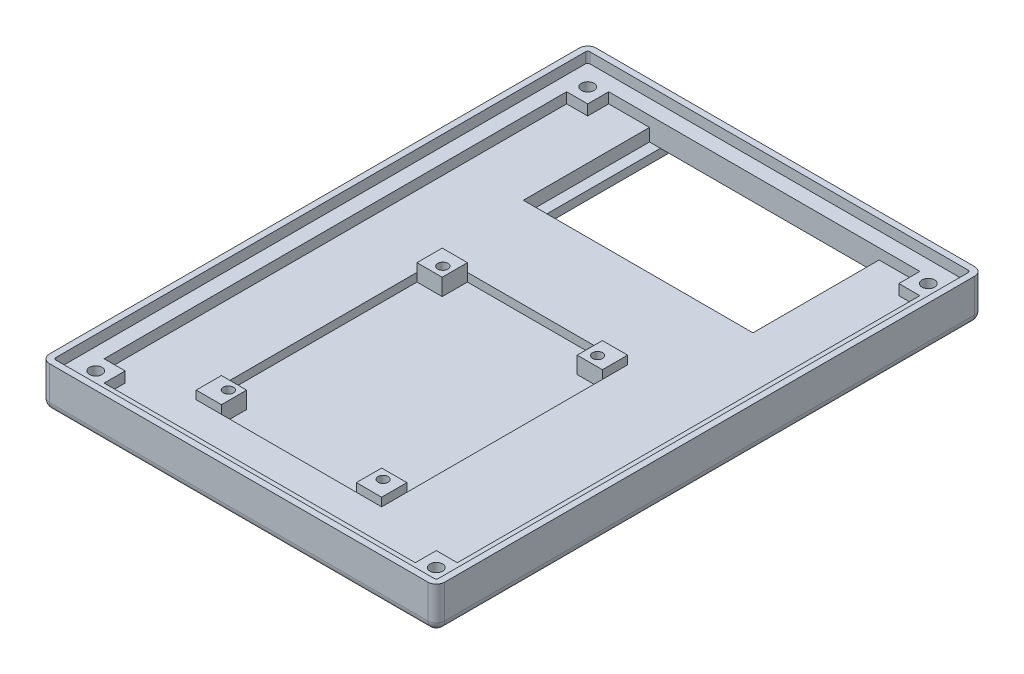
SolidWorks part; units mm, degrees
ref_plane "Front Plane" through (0, 0, 0) normal (0, 0, 1) x (1, 0, 0)
ref_plane "Top Plane" through (0, 0, 0) normal (0, 1, 0) x (1, 0, 0)
ref_plane "Right Plane" through (0, 0, 0) normal (1, 0, 0) x (0, 0, -1)
sketch "Sketch1" plane through (0, 0, 0) normal (0, 1, 0) x (1, 0, 0)
  line L1 (0, 0) -> (94, 0)
  line L2 (0, 0) -> (0, 130)
  line L3 (0, 130) -> (94, 130)
  line L4 (94, 0) -> (94, 130)
  dimension "D1" = 94
  dimension "D2" = 130
extrude "Boss-Extrude1" add sketch "Sketch1" along normal blind 5
sketch "Sketch2" plane through (0, 5, 0) normal (0, 1, 0) x (1, 0, 0)
  line L4 (5, 125) -> (5, 5)
  line L5 (5, 5) -> (89, 5)
  line L6 (89, 5) -> (89, 125)
  line L7 (89, 125) -> (5, 125)
  line L8 (0, 130) -> (0, 0)
  line L9 (0, 0) -> (94, 0)
  line L10 (94, 0) -> (94, 130)
  line L11 (94, 130) -> (0, 130)
  line L12 (0, 130) -> (0, 0)
  line L13 (0, 0) -> (94, 0)
  line L14 (94, 0) -> (94, 130)
  line L15 (94, 130) -> (0, 130)
  dimension "D1" = 0
  dimension "D2" = 5
extrude "Boss-Extrude2" add sketch "Sketch2" along normal blind 5
fillet "Fillet1" radius 2 8 edges at (0, 5, -130) (0, 5, 0) (94, 5, 0) (47, 0, 0) (0, 0, -65) (94, 0, -65) (47, 0, -130) (94, 5, -130)
sketch "Sketch3" plane through (0, 5, 0) normal (0, 1, 0) x (1, 0, 0)
  line L0 (5, 125) -> (5, 5) construction
  line L1 (21.9, 73.5) -> (66, 73.5)
  line L2 (21.9, 73.5) -> (21.9, 15)
  line L3 (21.9, 15) -> (66, 15)
  line L4 (66, 73.5) -> (66, 15)
  line L11 (5, 5) -> (89, 5) construction
  dimension "D1" = 58.5
  dimension "D2" = 44.1
  dimension "D3" = 16.9
  dimension "D4" = 10
extrude "Cut-Extrude1" cut sketch "Sketch3" against normal blind 2
sketch "Sketch5" plane through (0, 3, 0) normal (0, 1, 0) x (1, 0, 0)
  line L0 (66, 73.5) -> (21.9, 73.5) construction
  line L1 (21.9, 73.5) -> (27.9, 73.5)
  line L2 (21.9, 73.5) -> (21.9, 67.5)
  line L3 (21.9, 67.5) -> (27.9, 67.5)
  line L4 (27.9, 73.5) -> (27.9, 67.5)
  line L5 (60, 73.5) -> (66, 73.5)
  line L6 (60, 73.5) -> (60, 67.5)
  line L7 (60, 67.5) -> (66, 67.5)
  line L8 (66, 73.5) -> (66, 67.5)
  line L9 (60, 21) -> (66, 21)
  line L10 (60, 21) -> (60, 15)
  line L11 (60, 15) -> (66, 15)
  line L12 (66, 21) -> (66, 15)
  line L13 (21.9, 21) -> (27.9, 21)
  line L14 (21.9, 21) -> (21.9, 15)
  line L15 (21.9, 15) -> (27.9, 15)
  line L16 (27.9, 21) -> (27.9, 15)
  line L17 (21.9, 73.5) -> (21.9, 15) construction
  line L18 (66, 15) -> (66, 73.5) construction
  line L19 (21.9, 15) -> (66, 15) construction
  dimension "D1" = 6
  dimension "D2" = 6
  dimension "D3" = 6
  dimension "D4" = 6
  dimension "D5" = 6
  dimension "D6" = 6
  dimension "D7" = 6
  dimension "D8" = 6
extrude "Boss-Extrude4" add sketch "Sketch5" along normal blind 4
sketch "Sketch7" plane through (0, 7, 0) normal (0, 1, 0) x (1, 0, 0)
  circle A0 centre (25.71, 69.839) radius 1.2
  circle A1 centre (62.5146, 69.839) radius 1.2
  circle A2 centre (62.5146, 18.8358) radius 1.2
  circle A3 centre (25.71, 18.8358) radius 1.2
  point P1 (0, 0)
  point P12 (0, 0)
  point P14 (0, 0)
  point P16 (0, 0)
  point P18 (0, 0)
extrude "Cut-Extrude2" cut sketch "Sketch7" against normal blind 3
sketch "Sketch8" plane through (0, 5, 0) normal (0, 1, 0) x (1, 0, 0)
  line L1 (19.7, 95) -> (74.3, 95)
  line L2 (19.7, 95) -> (19.7, 125)
  line L3 (19.7, 125) -> (74.3, 125)
  line L4 (74.3, 95) -> (74.3, 125)
  line L5 (89, 125) -> (5, 125) construction
  line L6 (89, 125) -> (5, 125) construction
  point P4 (47, 125)
  point P9 (47, 95)
  dimension "D1" = 30
  dimension "D2" = 54.6
extrude "Cut-Extrude3" cut sketch "Sketch8" against normal blind 3
sketch "Sketch9" plane through (0, 2, 0) normal (0, 1, 0) x (1, 0, 0)
  line L0 (19.7, 95) -> (74.3, 95) construction
  line L1 (22.3, 96.5) -> (71.7, 96.5)
  line L2 (22.3, 96.5) -> (22.3, 123.5)
  line L3 (22.3, 123.5) -> (71.7, 123.5)
  line L4 (71.7, 96.5) -> (71.7, 123.5)
  line L5 (74.3, 125) -> (19.7, 125) construction
  line L6 (19.7, 125) -> (19.7, 95) construction
  line L7 (74.3, 95) -> (74.3, 125) construction
  dimension "D1" = 1.5
  dimension "D2" = 1.5
  dimension "D3" = 2.6
  dimension "D4" = 2.6
extrude "Cut-Extrude4" cut sketch "Sketch9" against normal blind 2
sketch "Sketch10" plane through (0, 0, 0) normal (0, -1, 0) x (1, 0, 0)
  line L1 (71.7, -123.5) -> (22.3, -123.5)
  line L2 (71.7, -123.5) -> (71.7, -130.1195)
  line L3 (71.7, -130.1195) -> (22.3, -130.1195)
  line L4 (22.3, -123.5) -> (22.3, -130.1195)
  line L5 (22.3, -123.5) -> (22.3, -96.5) construction
  line L6 (71.7, -96.5) -> (71.7, -123.5) construction
  line L7 (71.7, -123.5) -> (22.3, -123.5) construction
extrude "Cut-Extrude5" cut sketch "Sketch10" against normal blind 2
sketch "Sketch11" plane through (0, 0, -96.5) normal (0, 0, -1) x (-1, 0, 0)
  line L0 (-22.3, 0) -> (-71.7, 0) construction
  line L1 (-49.5, 1.5) -> (-44.5, 1.5)
  line L2 (-49.5, 1.5) -> (-49.5, 0.5)
  line L3 (-49.5, 0.5) -> (-44.5, 0.5)
  line L4 (-44.5, 1.5) -> (-44.5, 0.5)
  line L5 (-71.7, 0) -> (-71.7, 2) construction
  point P6 (-47, 0)
  point P7 (-47, 0.5)
  point P10 (-71.7, 1)
  point P11 (-49.5, 1)
  dimension "D1" = 5
  dimension "D2" = 1
extrude "Cut-Extrude6" cut sketch "Sketch11" against normal blind 3
sketch "Sketch14" plane through (0, 10, 0) normal (0, 1, 0) x (1, 0, 0)
  line L8 (89, 5) -> (89, 125)
  line L9 (89, 125) -> (5, 125)
  line L10 (5, 125) -> (5, 5)
  line L11 (5, 5) -> (89, 5)
  line L12 (89, 5) -> (89, 125)
  line L13 (89, 125) -> (5, 125)
  line L14 (5, 125) -> (5, 5)
  line L15 (5, 5) -> (89, 5)
  line L20 (92.5, 2) -> (92.5, 128)
  line L21 (92, 128.5) -> (2, 128.5)
  line L22 (1.5, 128) -> (1.5, 2)
  line L23 (2, 1.5) -> (92, 1.5)
  line L24 (92.5, 2) -> (92.5, 128)
  line L25 (92, 128.5) -> (2, 128.5)
  line L26 (1.5, 128) -> (1.5, 2)
  line L27 (2, 1.5) -> (92, 1.5)
  arc A12 (92.5, 128) -> (92, 128.5) centre (92, 128) ccw
  arc A13 (2, 128.5) -> (1.5, 128) centre (2, 128) ccw
  arc A14 (1.5, 2) -> (2, 1.5) centre (2, 2) ccw
  arc A15 (92, 1.5) -> (92.5, 2) centre (92, 2) ccw
  arc A16 (92.5, 128) -> (92, 128.5) centre (92, 128) ccw
  arc A17 (2, 128.5) -> (1.5, 128) centre (2, 128) ccw
  arc A18 (1.5, 2) -> (2, 1.5) centre (2, 2) ccw
  arc A19 (92, 1.5) -> (92.5, 2) centre (92, 2) ccw
  dimension "D1" = 5
  dimension "D2" = 1.5
extrude "Cut-Extrude8" cut sketch "Sketch14" against normal blind 2.5
sketch "Sketch15" plane through (0, 5, 0) normal (0, 1, 0) x (1, 0, 0)
  line L1 (89, 120) -> (84, 120)
  line L2 (89, 120) -> (89, 125)
  line L3 (89, 125) -> (84, 125)
  line L4 (84, 120) -> (84, 125)
  line L5 (10, 120) -> (5, 120)
  line L6 (10, 120) -> (10, 125)
  line L7 (10, 125) -> (5, 125)
  line L8 (5, 120) -> (5, 125)
  line L9 (10, 5) -> (5, 5)
  line L10 (10, 5) -> (10, 10)
  line L11 (10, 10) -> (5, 10)
  line L12 (5, 5) -> (5, 10)
  line L13 (89, 5) -> (84, 5)
  line L14 (89, 5) -> (89, 10)
  line L15 (89, 10) -> (84, 10)
  line L16 (84, 5) -> (84, 10)
  line L17 (89, 125) -> (74.3, 125) construction
  line L18 (89, 5) -> (89, 125) construction
  line L19 (19.7, 125) -> (5, 125) construction
  line L20 (5, 125) -> (5, 5) construction
  line L22 (5, 5) -> (89, 5) construction
  dimension "D1" = 5
  dimension "D2" = 5
  dimension "D3" = 5
  dimension "D4" = 5
  dimension "D5" = 5
  dimension "D6" = 5
  dimension "D7" = 5
  dimension "D8" = 5
extrude "Boss-Extrude5" add sketch "Sketch15" along normal blind 2.5
sketch "Sketch16" plane through (0, 7.5, 0) normal (0, 1, 0) x (1, 0, 0)
  line L0 (10, 120) -> (10, 125) construction
  line L2 (5, 120) -> (10, 120) construction
  line L4 (84, 125) -> (84, 120) construction
  line L5 (89, 10) -> (84, 10) construction
  circle A0 centre (6.5, 123.5) radius 1.5
  circle A1 centre (87.5, 123.5) radius 1.5
  circle A2 centre (87.5, 6.5) radius 1.5
  circle A3 centre (6.5, 6.5) radius 1.5
  point P0 (6.5, 123.5)
  point P1 (87.5, 123.5)
  point P2 (87.5, 6.5)
  point P3 (6.5, 6.5)
  dimension "D5" = 3
  dimension "D6" = 3
  dimension "D7" = 3
  dimension "D8" = 3
  dimension "D1" = 3.5
  dimension "D2" = 3.5
  dimension "D3" = 3.5
  dimension "D4" = 3.5
extrude "Cut-Extrude9" cut sketch "Sketch16" against normal through all
sketch "Sketch17" plane through (0, 0, 0) normal (0, -1, 0) x (1, 0, 0)
  circle A0 centre (6.5, -6.5) radius 2.8
  circle A1 centre (87.5, -6.5) radius 2.8
  circle A2 centre (87.5, -123.5) radius 2.8
  circle A3 centre (6.5, -123.5) radius 2.8
  dimension "D1" = 5.6
  dimension "D2" = 5.6
  dimension "D3" = 5.6
  dimension "D4" = 5.6
extrude "Cut-Extrude10" cut sketch "Sketch17" against normal blind 3
sketch "Sketch18" plane through (0, 0, 0) normal (0, -1, 0) x (1, 0, 0)
  circle A0 centre (6.5, -123.5) radius 4
  circle A1 centre (87.5, -123.5) radius 4
  circle A2 centre (87.5, -6.5) radius 4
  circle A3 centre (6.5, -6.5) radius 4
  circle A4 centre (87.5, -123.5) radius 2.8 construction
  circle A5 centre (6.5, -123.5) radius 2.8 construction
  circle A6 centre (6.5, -6.5) radius 2.8 construction
  circle A7 centre (87.5, -6.5) radius 2.8 construction
  dimension "D1" = 8
  dimension "D2" = 8
  dimension "D3" = 8
  dimension "D4" = 8
extrude "Cut-Extrude11" cut sketch "Sketch18" against normal blind 2
